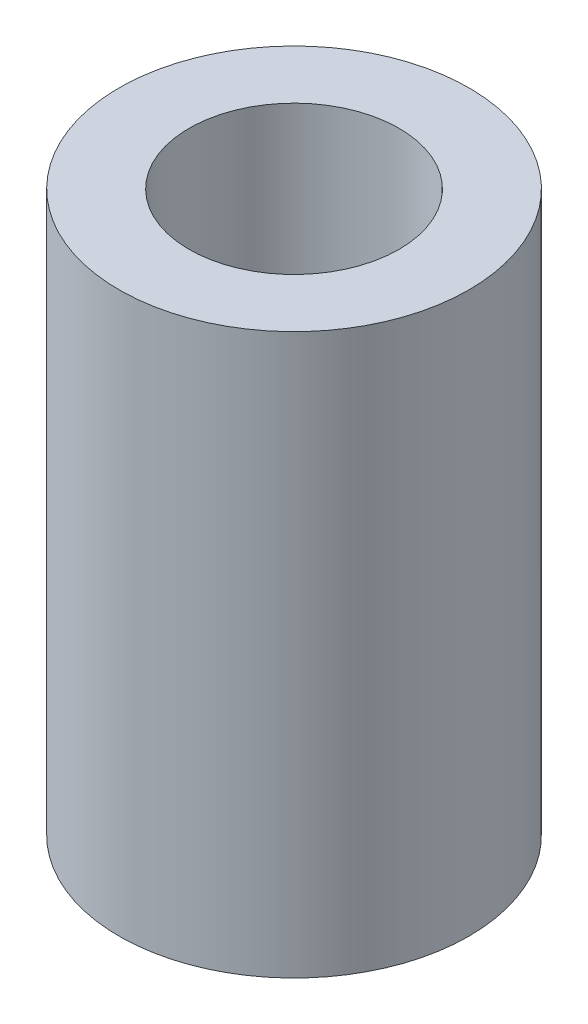
SolidWorks part; units mm, degrees
ref_plane "Front Plane" through (0, 0, 0) normal (0, 0, 1) x (1, 0, 0)
ref_plane "Top Plane" through (0, 0, 0) normal (0, 1, 0) x (1, 0, 0)
ref_plane "Right Plane" through (0, 0, 0) normal (1, 0, 0) x (0, 0, -1)
sketch "Sketch1" plane through (0, 0, 0) normal (0, 1, 0) x (1, 0, 0)
  circle A0 centre (0, 0) radius 6
  dimension "D1" = 12
extrude "Extrude-Thin1" add sketch "Sketch1" along normal blind 24 thin thin type mid plane wall 3
